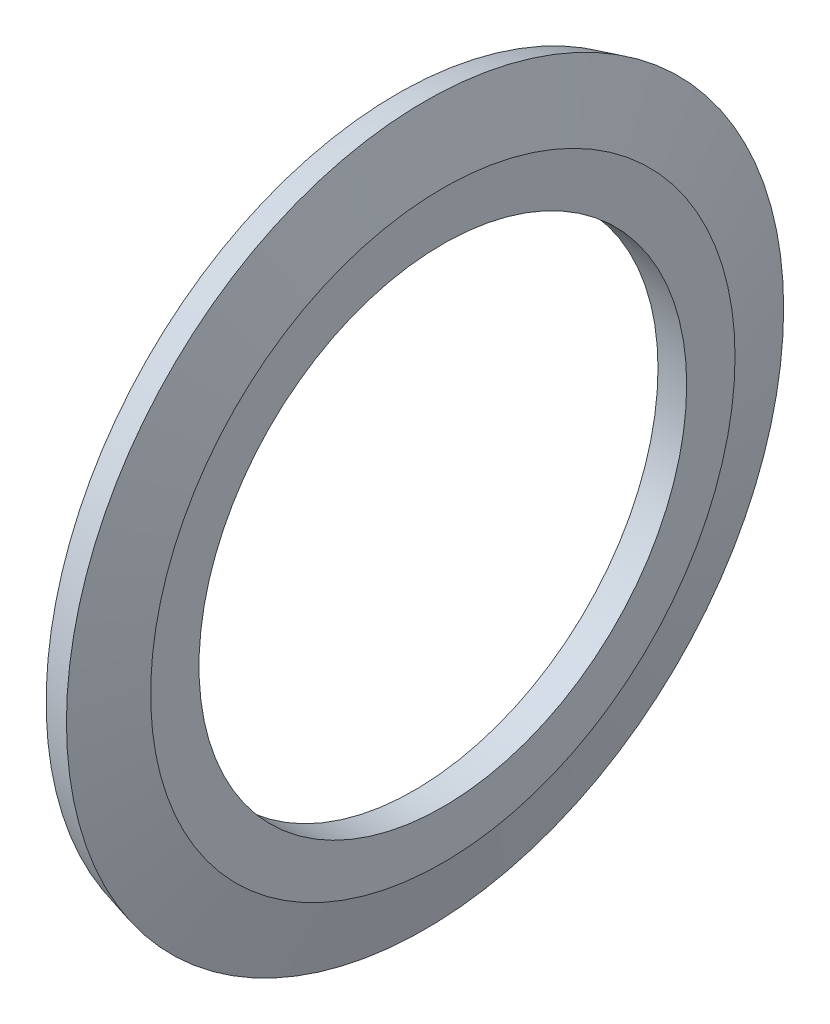
SolidWorks part; units mm, degrees
ref_plane "Front Plane" through (0, 0, 0) normal (0, 0, 1) x (1, 0, 0)
ref_plane "Top Plane" through (0, 0, 0) normal (0, 1, 0) x (1, 0, 0)
ref_plane "Right Plane" through (0, 0, 0) normal (1, 0, 0) x (0, 0, -1)
sketch "Sketch1" plane through (0, 0, 0) normal (0, 0, 1) x (1, 0, 0)
  line L0 (1, 8.5) -> (0, 8.5)
  line L1 (0, 8.5) -> (0, 10.0533)
  line L2 (1, 8.5) -> (1, 10.185)
  line L3 (1, 10.185) -> (0.3797, 12.5)
  line L4 (0.3797, 12.5) -> (-0.5862, 12.2412)
  line L5 (-0.5862, 12.2412) -> (0, 10.0533)
  line L6 (1, 0) -> (0, 0) construction
  dimension "D1" = 1
  dimension "D2" = 15
  dimension "E" = 17
  dimension "P.D." = 20.37
  dimension "F_1" = 25
revolve "Revolve1" add sketch "Sketch1" angle 360 about L6
sketch "Sketch2" [suppressed] plane through (0, 0, 0) normal (0, 0, 1) x (1, 0, 0)
  line L0 (-0.4389, 0) -> (0, 0) construction
  line L1 (-0.4389, 18) -> (1, 18)
  line L2 (-0.4389, 18) -> (-0.4389, 16.5)
  line L3 (-0.4389, 16.5) -> (1, 16.5)
  line L4 (1, 18) -> (1, 16.5)
  line L7 (1, -16.235) -> (1, 16.235) construction
  line L8 (-0.4389, 17.7412) -> (-0.4389, -17.7412) construction
  dimension "FC" = 40
revolve "Cut-Revolve1" [suppressed] cut sketch "Sketch2" angle 360 about L0
